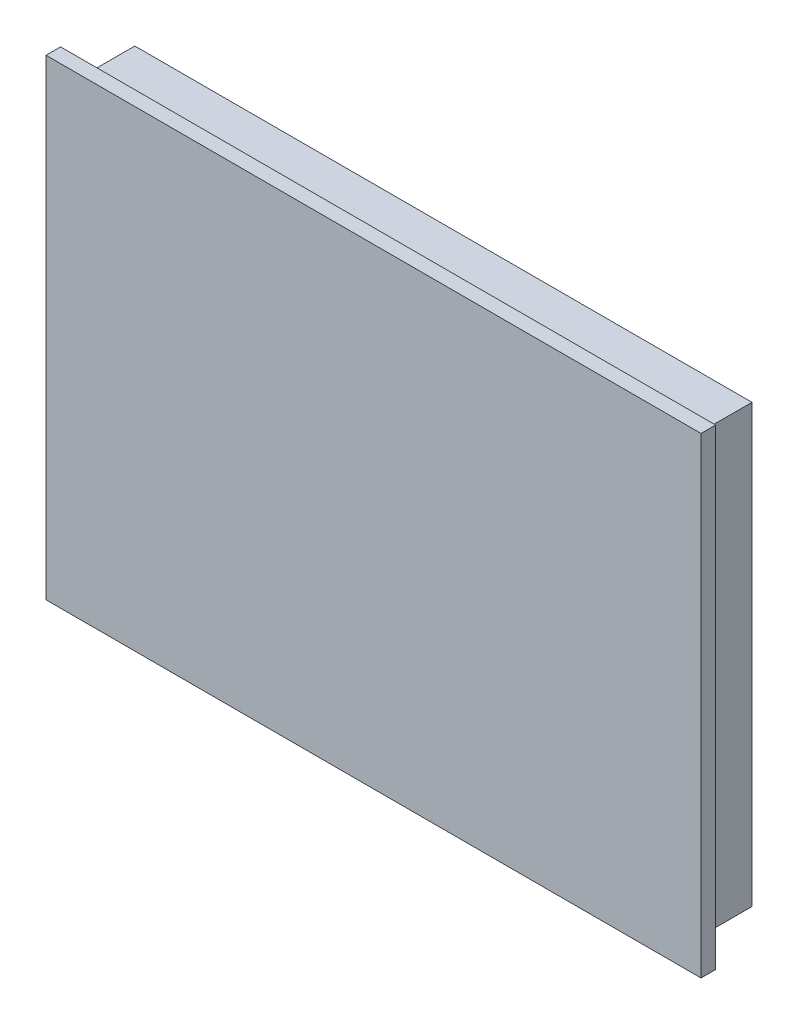
SolidWorks part; units mm, degrees
ref_plane "前视基准面" through (0, 0, 0) normal (0, 0, 1) x (1, 0, 0)
ref_plane "上视基准面" through (0, 0, 0) normal (0, 1, 0) x (1, 0, 0)
ref_plane "右视基准面" through (0, 0, 0) normal (1, 0, 0) x (0, 0, -1)
sketch "草图1" plane through (0, 0, 0) normal (0, 0, 1) x (1, 0, 0)
  line L0 (0, 0) -> (225, 0)
  line L1 (225, 0) -> (225, 162)
  line L2 (225, 162) -> (0, 162)
  line L3 (0, 162) -> (0, 0)
  dimension "D1" = 225
  dimension "D2" = 162
extrude "凸台-拉伸1" add sketch "草图1" along normal blind 5
sketch "草图3" plane through (0, 0, 0) normal (0, 0, -1) x (-1, 0, 0)
  line L3 (-218.5, 156) -> (-6.5, 156)
  line L4 (-6.5, 156) -> (-6.5, 6)
  line L5 (-6.5, 6) -> (-218.5, 6)
  line L6 (-218.5, 6) -> (-218.5, 156)
extrude "凸台-拉伸2" add sketch "草图3" along normal blind 19
sketch "草图4" plane through (0, 0, -19) normal (0, 0, -1) x (-1, 0, 0)
  line L7 (-112.5, 136) -> (-188, 136)
  line L8 (-188, 136) -> (-188, 26)
  line L9 (-188, 26) -> (-37, 26)
  line L10 (-37, 26) -> (-37, 136)
  line L11 (-37, 136) -> (-112.5, 136)
extrude "凸台-拉伸3" add sketch "草图4" along normal blind 10
sketch "草图5" plane through (0, 0, -29) normal (0, 0, -1) x (-1, 0, 0)
  line L0 (-188, 121) -> (-188, 55.3502)
  line L2 (-168, 55.3502) -> (-188, 55.3502)
  line L3 (-37, 121) -> (-57, 121)
  line L5 (-37, 121) -> (-37, 57)
  line L6 (-37, 26) -> (-37, 136) construction
  line L7 (-37, 57) -> (-57, 57)
  line L8 (-188, 136) -> (-188, 26) construction
  line L10 (-37, 26) -> (-37, 136) construction
  line L11 (-57, 57) -> (-57, 121)
  line L14 (-188, 121) -> (-168, 121)
  line L15 (-168, 121) -> (-168, 55.3502)
extrude "切除-拉伸1" cut sketch "草图5" against normal blind 10
sketch "草图7" plane through (0, 0, -19) normal (0, 0, -1) x (-1, 0, 0)
  line L0 (-54, 117.8838) -> (-46, 117.8838)
  line L2 (-46, 117.8838) -> (-46, 105.8838)
  line L6 (-46, 105.8838) -> (-54, 105.8838)
  line L7 (-54, 105.8838) -> (-54, 117.8838)
  line L9 (-54, 84.5885) -> (-54, 72.0682)
  line L10 (-45, 72.7349) -> (-45, 83.9219)
  line L15 (-50.3492, 87.5171) -> (-47.3492, 86.8504)
  line L16 (-50.3492, 69.1397) -> (-47.3492, 69.8063)
  circle A0 centre (-50, 115.5455) radius 0.2626
  circle A1 centre (-50, 108.2996) radius 0.291
  circle A2 centre (-50, 65.3599) radius 2
  arc A3 (-50.3492, 87.5171) -> (-54, 84.5885) centre (-51, 84.5885) ccw
  arc A4 (-54, 72.0682) -> (-50.3492, 69.1397) centre (-51, 72.0682) ccw
  arc A5 (-45, 72.7349) -> (-47.3492, 69.8063) centre (-48, 72.7349) cw
  arc A6 (-45, 83.9219) -> (-47.3492, 86.8504) centre (-48, 83.9219) ccw
  circle A7 centre (-50, 91.2971) radius 2
  dimension "D1" = 3
  dimension "D2" = 3
extrude "凸台-拉伸4" add sketch "草图7" along normal blind 5 from surface at 0 starting at face at (112.5, 81, -19)
sketch "草图9" plane through (0, 0, 5) normal (0, 0, 1) x (1, 0, 0)
  line L2 (35.5, 125) -> (190.5, 125)
  line L3 (11.5, 155) -> (213.5, 155)
  line L4 (213.5, 155) -> (213.5, 7)
  line L5 (213.5, 7) -> (11.5, 7)
  line L6 (11.5, 7) -> (11.5, 155)
  line L7 (190.5, 125) -> (190.5, 37)
  line L8 (190.5, 37) -> (35.5, 37)
  line L9 (35.5, 37) -> (35.5, 125)
sketch "草图10" plane through (0, 0, 5) normal (0, 0, 1) x (1, 0, 0)
  text T0 "<b>MCGS</b>"
